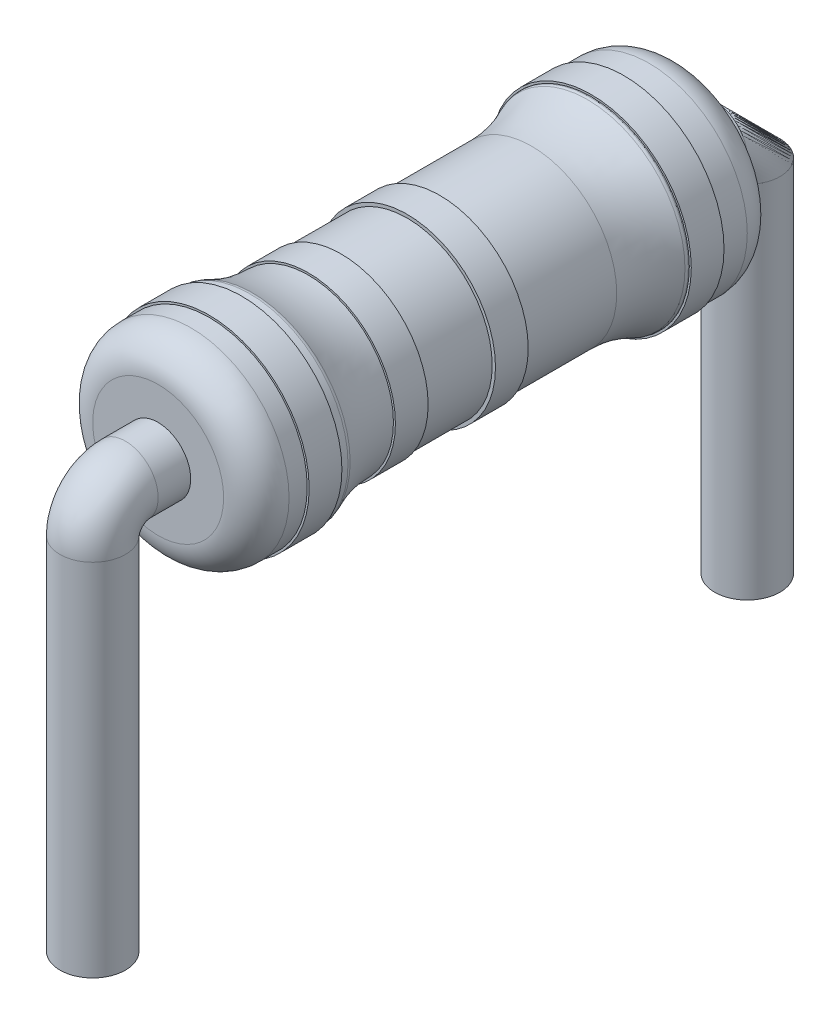
SolidWorks part; units mm, degrees
ref_plane "Front Plane" through (0, 0, 0) normal (0, 0, 1) x (1, 0, 0)
ref_plane "Top Plane" through (0, 0, 0) normal (0, 1, 0) x (1, 0, 0)
ref_plane "Right Plane" through (0, 0, 0) normal (1, 0, 0) x (0, 0, -1)
sketch "Sketch1" plane through (0, 0, 0) normal (1, 0, 0) x (0, 0, -1)
  line L0 (-30.9469, 0) -> (36.7722, 0) construction
  line L1 (2.6, 1.5) -> (3.5, 1.5)
  line L2 (-3.5, 1.5) -> (-2.6, 1.5)
  line L3 (-4, 1) -> (-4, 0)
  line L4 (-4, 0) -> (4, 0)
  line L5 (4, 1) -> (4, 0)
  line L7 (-2.5, 1.4) -> (-2.5, 1.3)
  line L8 (-2.5, 1.3) -> (2.5, 1.3)
  line L9 (2.5, 1.4) -> (2.5, 1.3)
  arc A0 (-3.5, 1.5) -> (-4, 1) centre (-3.5, 1) ccw
  arc A1 (-2.6, 1.5) -> (-2.5, 1.4) centre (-2.6, 1.4) cw
  arc A2 (2.6, 1.5) -> (2.5, 1.4) centre (2.6, 1.4) ccw
  arc A3 (3.5, 1.5) -> (4, 1) centre (3.5, 1) cw
  point P7 (0, 0)
  point P14 (0, 1.3)
  dimension "D3" = 0.5
  dimension "D6" = 0.1
  dimension "D7" = 0.5
  dimension "D1" = 8
  dimension "D2" = 1.5
  dimension "D4" = 5
  dimension "D5" = 0.2
revolve "Revolve1" add sketch "Sketch1" angle 360 about L0
fillet "Fillet1" radius 2 2 edges at (1.3, 0, -2.5) (1.3, 0, 2.5)
sketch "Sketch2" plane through (0, 0, 0) normal (1, 0, 0) x (0, 0, -1)
  line L0 (-2.1847, 0) -> (2.4452, 0) construction
  line L1 (-1.7056, -1.3) -> (-1.7056, 1.3) construction
  line L2 (-1.7056, 1.3) -> (-1.2056, 1.3)
  line L3 (-1.7056, 1.3) -> (-1.7056, 1.33)
  line L4 (-1.7056, 1.33) -> (-1.2056, 1.33)
  line L5 (-1.2056, 1.3) -> (-1.2056, 1.33)
  dimension "D1" = 0.5
revolve "Revolve2" add sketch "Sketch2" angle 360 about L0
sketch "Sketch3" plane through (0, 0, 0) normal (1, 0, 0) x (0, 0, -1)
  line L0 (-0.4894, 0) -> (0.7498, 0) construction
  line L2 (-0.1968, 1.35) -> (0.3032, 1.35)
  line L3 (-0.1968, 1.35) -> (-0.1968, 1.3)
  line L4 (-0.1968, 1.3) -> (0.3032, 1.3)
  line L5 (0.3032, 1.35) -> (0.3032, 1.3)
  dimension "D1" = 0.5
  dimension "D2" = 0.05
  dimension "D3" = 1.3
revolve "Revolve3" add sketch "Sketch3" angle 360 about L0
sketch "Sketch4" plane through (0, 0, 0) normal (1, 0, 0) x (0, 0, -1)
  line L0 (-0.4492, 0) -> (0.4962, 0) construction
  line L1 (-3.2228, 1.53) -> (-2.7228, 1.53)
  line L2 (-3.2228, 1.53) -> (-3.2228, 1.5)
  line L3 (-3.2228, 1.5) -> (-2.7228, 1.5)
  line L4 (-2.7228, 1.53) -> (-2.7228, 1.5)
  dimension "D1" = 0.5
  dimension "D2" = 0.03
  dimension "D3" = 1.5
revolve "Revolve4" add sketch "Sketch4" angle 360 about L0
sketch "Sketch5" plane through (0, 0, 0) normal (1, 0, 0) x (0, 0, -1)
  line L0 (-0.3134, 0) -> (0.3032, 0) construction
  line L1 (2.6145, 1.53) -> (3.1145, 1.53)
  line L2 (2.6145, 1.53) -> (2.6145, 1.5)
  line L3 (2.6145, 1.5) -> (3.1145, 1.5)
  line L4 (3.1145, 1.53) -> (3.1145, 1.5)
  line L5 (0.3032, -1.35) -> (0.3032, 1.35) construction
  dimension "D1" = 0.5
  dimension "D2" = 0.03
  dimension "D3" = 1.5
revolve "Revolve5" add sketch "Sketch5" angle 360 about L0
ref_plane "Plane1" through (0, 0, 4.0029) normal (0, 0, 1) x (1, 0, 0)
sketch "Sketch6" plane through (0, 0, 4.0029) normal (0, 0, 1) x (1, 0, 0)
  circle A0 centre (0, 0) radius 0.5
ref_plane "Plane2" through (0, -6, 0) normal (0, 1, 0) x (-1, 0, 0)
sketch "Sketch7" plane through (0, -6, 0) normal (0, 1, 0) x (-1, 0, 0)
  circle A0 centre (0, 5) radius 0.5
  dimension "D1" = 5
sketch "Sketch8" plane through (0, 0, 0) normal (1, 0, 0) x (0, 0, -1)
  line L0 (-4.0029, 0) -> (-4.5, 0)
  line L1 (-4.0029, 0.5) -> (-4.0029, -0.5) construction
  line L2 (-5, -0.5) -> (-5, -6)
  line L3 (-4.5, -6) -> (-5.5, -6) construction
  arc A0 (-4.5, 0) -> (-5, -0.5) centre (-4.5, -0.5) ccw
  dimension "D1" = 0.5
surface "Surface-Sweep1"
sketch "Sketch9" plane through (0, 0, -4) normal (0, 0, -1) x (-1, 0, 0)
  circle A0 centre (0, 0) radius 0.5
ref_plane "Plane4" through (0, -6, 0) normal (0, 1, 0) x (-1, 0, 0)
sketch "Sketch12" plane through (0, -6, 0) normal (0, 1, 0) x (-1, 0, 0)
  circle A0 centre (0, -5) radius 0.5
  dimension "D1" = 5
sketch "Sketch13" plane through (0, 0, 0) normal (1, 0, 0) x (0, 0, -1)
  line L0 (4, 0) -> (4.5, 0)
  line L1 (4, -0.5) -> (4, 0.5) construction
  line L2 (5, -0.5) -> (5, -6)
  line L3 (5.5, -6) -> (4.5, -6) construction
  arc A0 (4.5, 0) -> (5, -0.5) centre (4.5, -0.5) cw
  dimension "D1" = 0.5
surface "Surface-Sweep3"
